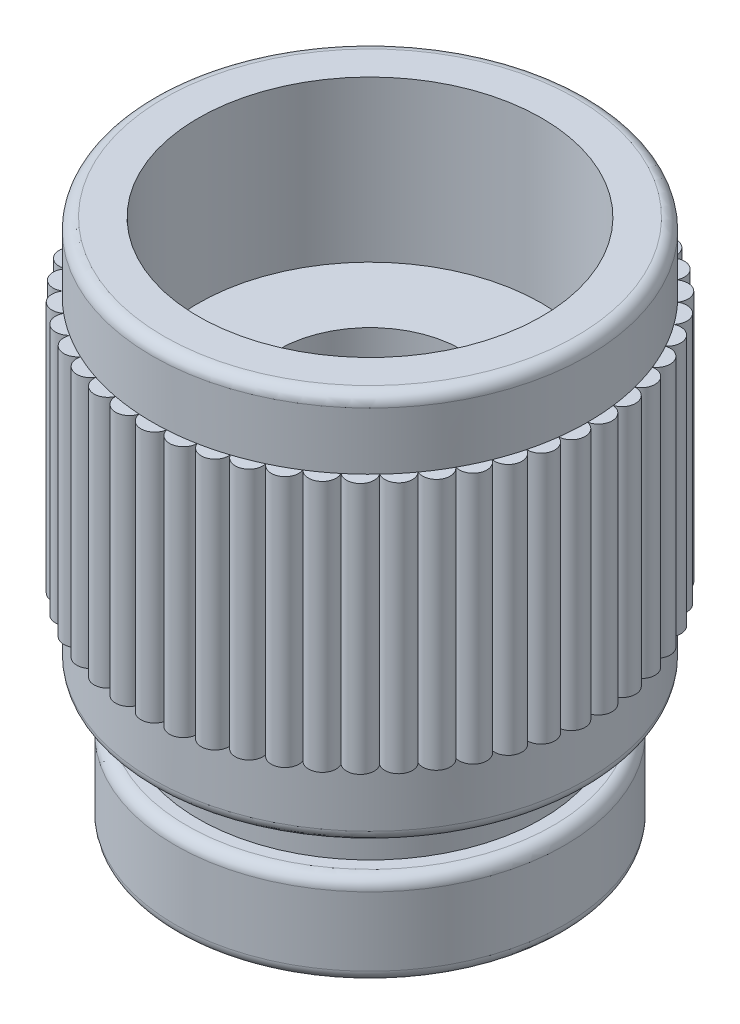
SolidWorks part; units mm, degrees
ref_plane "Plan de face" through (0, 0, 0) normal (0, 0, 1) x (1, 0, 0)
ref_plane "Plan de dessus" through (0, 0, 0) normal (0, 1, 0) x (1, 0, 0)
ref_plane "Plan de droite" through (0, 0, 0) normal (1, 0, 0) x (0, 0, -1)
sketch "Esquisse1" plane through (0, 0, 0) normal (0, 0, 1) x (1, 0, 0)
  line L0 (0, 0) -> (0, 8.5) construction
  line L1 (0, 8.5) -> (3.75, 8.5) construction
  line L2 (3.75, 8.5) -> (3.75, 0) construction
  line L3 (3.75, 0) -> (0, 0) construction
  line L4 (3.75, 8.5) -> (4.5, 8.5)
  line L5 (3.75, 8.5) -> (3.75, 5)
  line L6 (3.75, 5) -> (2, 5)
  line L7 (2, 5) -> (2, -2.75)
  line L8 (2.25, -3) -> (4, -3)
  line L9 (4.75, 8.25) -> (4.75, 0.25)
  line L10 (4.5, 0) -> (3.75, 0) construction
  line L11 (4.25, -2.75) -> (4.25, -1.25)
  line L12 (4, -1) -> (3.75, -1)
  line L13 (3.75, -1) -> (3.75, 0)
  line L14 (3.75, 0) -> (4.5, 0)
  arc A0 (4.75, 0.25) -> (4.5, 0) centre (4.5, 0.25) cw
  arc A1 (4.75, 8.25) -> (4.5, 8.5) centre (4.5, 8.25) ccw
  arc A2 (2.25, -3) -> (2, -2.75) centre (2.25, -2.75) cw
  arc A3 (4.25, -2.75) -> (4, -3) centre (4, -2.75) cw
  arc A4 (4.25, -1.25) -> (4, -1) centre (4, -1.25) ccw
  point P20 (2, -3)
  point P23 (4.25, -3)
  dimension "D4" = 0.25
  dimension "D11" = 0.25
  dimension "D1" = 8.5
  dimension "D2" = 7.5
  dimension "D3" = 9.5
  dimension "D5" = 3.5
  dimension "D6" = 4
  dimension "D7" = 8
  dimension "D8" = 2.25
  dimension "D9" = 1
  dimension "D10" = 0.75
revolve "Révolution1" add sketch "Esquisse1" angle 360 about L0
ref_plane "Plan1" through (0, 4.25, 0) normal (0, 1, 0) x (1, 0, 0)
sketch "Esquisse2" plane through (0, 4.25, 0) normal (0, 1, 0) x (1, 0, 0)
  line L0 (-0.2972, 4.7407) -> (-0.3129, 4.9902) construction
  line L1 (0, 5) -> (0, 0) construction
  arc A1 (-0.2972, 4.7407) -> (0.2972, 4.7407) centre (0, 4.7) cw
  circle A2 centre (0, 0) radius 5 construction
  circle A3 centre (0, 0) radius 4.75 construction
  arc A4 (-0.2972, 4.7407) -> (0.2972, 4.7407) centre (0, 0) cw
  arc A5 (0.2993, 4.7406) -> (0.889, 4.6661) centre (0.5891, 4.6629) cw
  arc A6 (0.2993, 4.7406) -> (0.889, 4.6661) centre (0, 0) cw
  arc A7 (0.8911, 4.6657) -> (1.4669, 4.5178) centre (1.1688, 4.5523) cw
  arc A8 (0.8911, 4.6657) -> (1.4669, 4.5178) centre (0, 0) cw
  arc A9 (1.4688, 4.5172) -> (2.0215, 4.2984) centre (1.7302, 4.3699) cw
  arc A10 (1.4688, 4.5172) -> (2.0215, 4.2984) centre (0, 0) cw
  arc A11 (2.0234, 4.2975) -> (2.5443, 4.0111) centre (2.2642, 4.1186) cw
  arc A12 (2.0234, 4.2975) -> (2.5443, 4.0111) centre (0, 0) cw
  arc A13 (2.546, 4.01) -> (3.027, 3.6606) centre (2.7626, 3.8024) cw
  arc A14 (2.546, 4.01) -> (3.027, 3.6606) centre (0, 0) cw
  arc A15 (3.0286, 3.6593) -> (3.4619, 3.2523) centre (3.2174, 3.4262) cw
  arc A16 (3.0286, 3.6593) -> (3.4619, 3.2523) centre (0, 0) cw
  arc A17 (3.4633, 3.2508) -> (3.8422, 2.7928) centre (3.6214, 2.9959) cw
  arc A18 (3.4633, 3.2508) -> (3.8422, 2.7928) centre (0, 0) cw
  arc A19 (3.8434, 2.7911) -> (4.162, 2.2892) centre (3.9683, 2.5184) cw
  arc A20 (3.8434, 2.7911) -> (4.162, 2.2892) centre (0, 0) cw
  arc A21 (4.163, 2.2874) -> (4.4161, 1.7495) centre (4.2527, 2.0012) cw
  arc A22 (4.163, 2.2874) -> (4.4161, 1.7495) centre (0, 0) cw
  arc A23 (4.4168, 1.7476) -> (4.6005, 1.1823) centre (4.47, 1.4524) cw
  arc A24 (4.4168, 1.7476) -> (4.6005, 1.1823) centre (0, 0) cw
  arc A25 (4.601, 1.1803) -> (4.7124, 0.5964) centre (4.6168, 0.8807) cw
  arc A26 (4.601, 1.1803) -> (4.7124, 0.5964) centre (0, 0) cw
  arc A27 (4.7127, 0.5943) -> (4.75, 0.001) centre (4.6907, 0.2951) cw
  arc A28 (4.7127, 0.5943) -> (4.75, 0.001) centre (0, 0) cw
  arc A29 (4.75, -0.001) -> (4.7127, -0.5943) centre (4.6907, -0.2951) cw
  arc A30 (4.75, -0.001) -> (4.7127, -0.5943) centre (0, 0) cw
  arc A31 (4.7124, -0.5964) -> (4.601, -1.1803) centre (4.6168, -0.8807) cw
  arc A32 (4.7124, -0.5964) -> (4.601, -1.1803) centre (0, 0) cw
  arc A33 (4.6005, -1.1823) -> (4.4168, -1.7476) centre (4.47, -1.4524) cw
  arc A34 (4.6005, -1.1823) -> (4.4168, -1.7476) centre (0, 0) cw
  arc A35 (4.4161, -1.7495) -> (4.163, -2.2874) centre (4.2527, -2.0012) cw
  arc A36 (4.4161, -1.7495) -> (4.163, -2.2874) centre (0, 0) cw
  arc A37 (4.162, -2.2892) -> (3.8434, -2.7911) centre (3.9683, -2.5184) cw
  arc A38 (4.162, -2.2892) -> (3.8434, -2.7911) centre (0, 0) cw
  arc A39 (3.8422, -2.7928) -> (3.4633, -3.2508) centre (3.6214, -2.9959) cw
  arc A40 (3.8422, -2.7928) -> (3.4633, -3.2508) centre (0, 0) cw
  arc A41 (3.4619, -3.2523) -> (3.0286, -3.6593) centre (3.2174, -3.4262) cw
  arc A42 (3.4619, -3.2523) -> (3.0286, -3.6593) centre (0, 0) cw
  arc A43 (3.027, -3.6606) -> (2.546, -4.01) centre (2.7626, -3.8024) cw
  arc A44 (3.027, -3.6606) -> (2.546, -4.01) centre (0, 0) cw
  arc A45 (2.5443, -4.0111) -> (2.0234, -4.2975) centre (2.2642, -4.1186) cw
  arc A46 (2.5443, -4.0111) -> (2.0234, -4.2975) centre (0, 0) cw
  arc A47 (2.0215, -4.2984) -> (1.4688, -4.5172) centre (1.7302, -4.3699) cw
  arc A48 (2.0215, -4.2984) -> (1.4688, -4.5172) centre (0, 0) cw
  arc A49 (1.4669, -4.5178) -> (0.8911, -4.6657) centre (1.1688, -4.5523) cw
  arc A50 (1.4669, -4.5178) -> (0.8911, -4.6657) centre (0, 0) cw
  arc A51 (0.889, -4.6661) -> (0.2993, -4.7406) centre (0.5891, -4.6629) cw
  arc A52 (0.889, -4.6661) -> (0.2993, -4.7406) centre (0, 0) cw
  arc A53 (0.2972, -4.7407) -> (-0.2972, -4.7407) centre (0, -4.7) cw
  arc A54 (0.2972, -4.7407) -> (-0.2972, -4.7407) centre (0, 0) cw
  arc A55 (-0.2993, -4.7406) -> (-0.889, -4.6661) centre (-0.5891, -4.6629) cw
  arc A56 (-0.2993, -4.7406) -> (-0.889, -4.6661) centre (0, 0) cw
  arc A57 (-0.8911, -4.6657) -> (-1.4669, -4.5178) centre (-1.1688, -4.5523) cw
  arc A58 (-0.8911, -4.6657) -> (-1.4669, -4.5178) centre (0, 0) cw
  arc A59 (-1.4688, -4.5172) -> (-2.0215, -4.2984) centre (-1.7302, -4.3699) cw
  arc A60 (-1.4688, -4.5172) -> (-2.0215, -4.2984) centre (0, 0) cw
  arc A61 (-2.0234, -4.2975) -> (-2.5443, -4.0111) centre (-2.2642, -4.1186) cw
  arc A62 (-2.0234, -4.2975) -> (-2.5443, -4.0111) centre (0, 0) cw
  arc A63 (-2.546, -4.01) -> (-3.027, -3.6606) centre (-2.7626, -3.8024) cw
  arc A64 (-2.546, -4.01) -> (-3.027, -3.6606) centre (0, 0) cw
  arc A65 (-3.0286, -3.6593) -> (-3.4619, -3.2523) centre (-3.2174, -3.4262) cw
  arc A66 (-3.0286, -3.6593) -> (-3.4619, -3.2523) centre (0, 0) cw
  arc A67 (-3.4633, -3.2508) -> (-3.8422, -2.7928) centre (-3.6214, -2.9959) cw
  arc A68 (-3.4633, -3.2508) -> (-3.8422, -2.7928) centre (0, 0) cw
  arc A69 (-3.8434, -2.7911) -> (-4.162, -2.2892) centre (-3.9683, -2.5184) cw
  arc A70 (-3.8434, -2.7911) -> (-4.162, -2.2892) centre (0, 0) cw
  arc A71 (-4.163, -2.2874) -> (-4.4161, -1.7495) centre (-4.2527, -2.0012) cw
  arc A72 (-4.163, -2.2874) -> (-4.4161, -1.7495) centre (0, 0) cw
  arc A73 (-4.4168, -1.7476) -> (-4.6005, -1.1823) centre (-4.47, -1.4524) cw
  arc A74 (-4.4168, -1.7476) -> (-4.6005, -1.1823) centre (0, 0) cw
  arc A75 (-4.601, -1.1803) -> (-4.7124, -0.5964) centre (-4.6168, -0.8807) cw
  arc A76 (-4.601, -1.1803) -> (-4.7124, -0.5964) centre (0, 0) cw
  arc A77 (-4.7127, -0.5943) -> (-4.75, -0.001) centre (-4.6907, -0.2951) cw
  arc A78 (-4.7127, -0.5943) -> (-4.75, -0.001) centre (0, 0) cw
  arc A79 (-4.75, 0.001) -> (-4.7127, 0.5943) centre (-4.6907, 0.2951) cw
  arc A80 (-4.75, 0.001) -> (-4.7127, 0.5943) centre (0, 0) cw
  arc A81 (-4.7124, 0.5964) -> (-4.601, 1.1803) centre (-4.6168, 0.8807) cw
  arc A82 (-4.7124, 0.5964) -> (-4.601, 1.1803) centre (0, 0) cw
  arc A83 (-4.6005, 1.1823) -> (-4.4168, 1.7476) centre (-4.47, 1.4524) cw
  arc A84 (-4.6005, 1.1823) -> (-4.4168, 1.7476) centre (0, 0) cw
  arc A85 (-4.4161, 1.7495) -> (-4.163, 2.2874) centre (-4.2527, 2.0012) cw
  arc A86 (-4.4161, 1.7495) -> (-4.163, 2.2874) centre (0, 0) cw
  arc A87 (-4.162, 2.2892) -> (-3.8434, 2.7911) centre (-3.9683, 2.5184) cw
  arc A88 (-4.162, 2.2892) -> (-3.8434, 2.7911) centre (0, 0) cw
  arc A89 (-3.8422, 2.7928) -> (-3.4633, 3.2508) centre (-3.6214, 2.9959) cw
  arc A90 (-3.8422, 2.7928) -> (-3.4633, 3.2508) centre (0, 0) cw
  arc A91 (-3.4619, 3.2523) -> (-3.0286, 3.6593) centre (-3.2174, 3.4262) cw
  arc A92 (-3.4619, 3.2523) -> (-3.0286, 3.6593) centre (0, 0) cw
  arc A93 (-3.027, 3.6606) -> (-2.546, 4.01) centre (-2.7626, 3.8024) cw
  arc A94 (-3.027, 3.6606) -> (-2.546, 4.01) centre (0, 0) cw
  arc A95 (-2.5443, 4.0111) -> (-2.0234, 4.2975) centre (-2.2642, 4.1186) cw
  arc A96 (-2.5443, 4.0111) -> (-2.0234, 4.2975) centre (0, 0) cw
  arc A97 (-2.0215, 4.2984) -> (-1.4688, 4.5172) centre (-1.7302, 4.3699) cw
  arc A98 (-2.0215, 4.2984) -> (-1.4688, 4.5172) centre (0, 0) cw
  arc A99 (-1.4669, 4.5178) -> (-0.8911, 4.6657) centre (-1.1688, 4.5523) cw
  arc A100 (-1.4669, 4.5178) -> (-0.8911, 4.6657) centre (0, 0) cw
  arc A101 (-0.889, 4.6661) -> (-0.2993, 4.7406) centre (-0.5891, 4.6629) cw
  arc A102 (-0.889, 4.6661) -> (-0.2993, 4.7406) centre (0, 0) cw
  point P161 (0, 0)
  dimension "D1" = 10
  dimension "D2" = 0.3
  dimension "D3" = 50
extrude "Boss.-Extru.1" add sketch "Esquisse2" along normal mid plane 5.5
